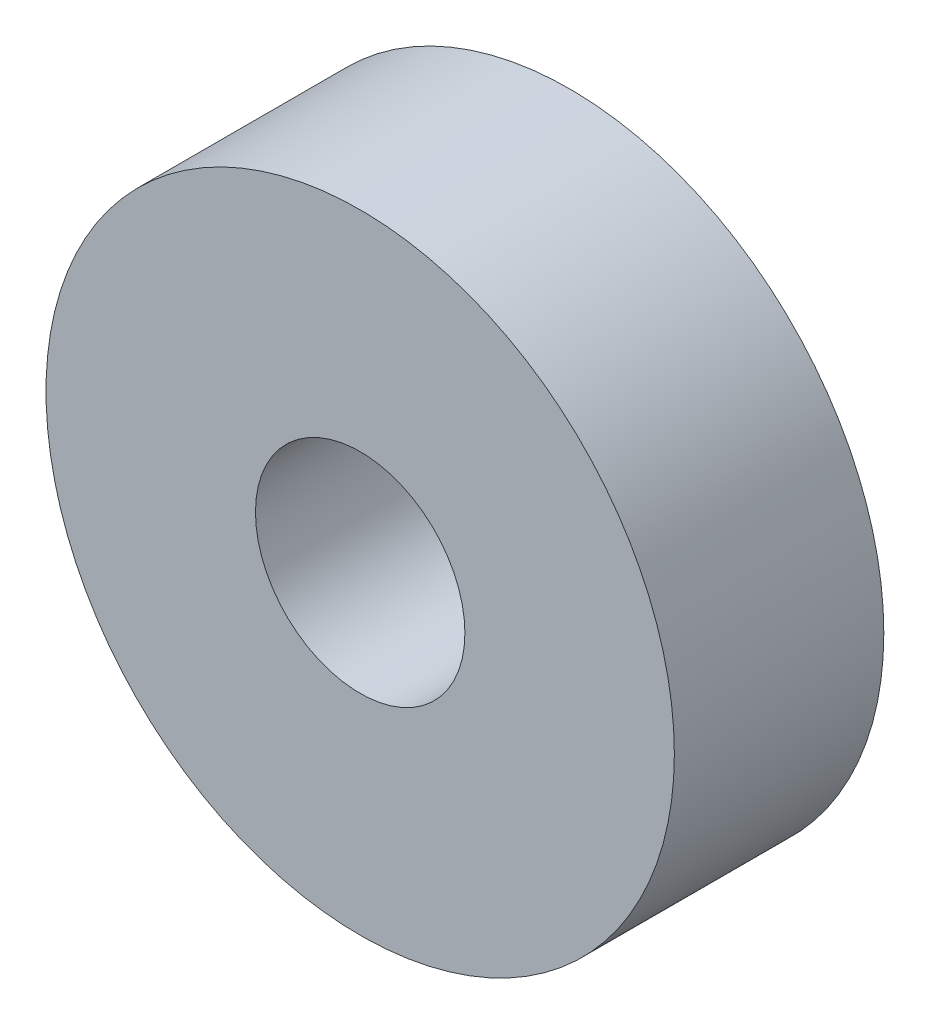
SolidWorks part; units mm, degrees
ref_plane "Front Plane" through (0, 0, 0) normal (0, 0, 1) x (1, 0, 0)
ref_plane "Top Plane" through (0, 0, 0) normal (0, 1, 0) x (1, 0, 0)
ref_plane "Right Plane" through (0, 0, 0) normal (1, 0, 0) x (0, 0, -1)
sketch "Sketch1" plane through (0, 0, 0) normal (0, 0, 1) x (1, 0, 0)
  circle A0 centre (0, 0) radius 12.7
  circle A1 centre (0, 0) radius 38.1
  dimension "D1" = 25.4
  dimension "D2" = 76.2
extrude "Boss-Extrude1" add sketch "Sketch1" along normal blind 25.4
sketch "Sketch2" plane through (0, 0, 0) normal (0, 0, -1) x (-1, 0, 0)
  line L1 (-14.6647, 25.4) -> (-29.3294, 0)
  line L2 (-29.3294, 0) -> (-14.6647, -25.4)
  line L3 (-14.6647, -25.4) -> (14.6647, -25.4)
  line L4 (14.6647, -25.4) -> (29.3294, 0)
  line L5 (29.3294, 0) -> (14.6647, 25.4)
  line L6 (14.6647, 25.4) -> (-14.6647, 25.4)
  circle A1 centre (0, 0) radius 25.4 construction
  dimension "D1" = 50.8
sketch "Sketch3" plane through (0, 0, 0) normal (0, 1, 0) x (1, 0, 0)
  line L1 (-35.6794, 0) -> (-22.9794, 0)
  line L2 (-35.6794, 0) -> (-35.6794, -3.175)
  line L3 (-32.5044, -6.35) -> (-26.1544, -6.35)
  line L4 (-22.9794, 0) -> (-22.9794, -3.175)
  arc A0 (-26.1544, -6.35) -> (-22.9794, -3.175) centre (-26.1544, -3.175) ccw
  arc A1 (-35.6794, -3.175) -> (-32.5044, -6.35) centre (-32.5044, -3.175) ccw
  point P0 (-29.3294, -3.175)
  point P1 (0, 0)
  point P14 (-29.3294, 0)
  dimension "D3" = 3.175
  dimension "D1" = 12.7
  dimension "D2" = 6.35
  dimension "D4" = 3.175
  dimension "D5" = 3.175
sweep "Cut-Sweep2" cut profiles "Sketch3" path "Sketch2"
